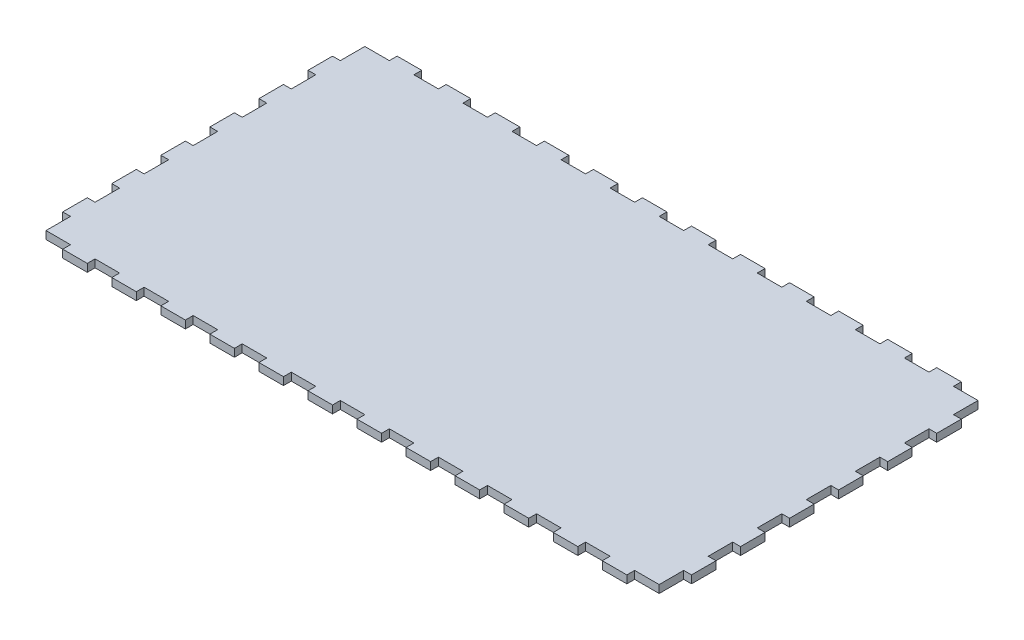
SolidWorks part; units mm, degrees
ref_plane "Plan de face" through (0, 0, 0) normal (0, 0, 1) x (1, 0, 0)
ref_plane "Plan de dessus" through (0, 0, 0) normal (0, 1, 0) x (1, 0, 0)
ref_plane "Plan de droite" through (0, 0, 0) normal (1, 0, 0) x (0, 0, -1)
sketch "Esquisse1" plane through (0, 0, 0) normal (0, 1, 0) x (1, 0, 0)
  line L1 (0, 0) -> (250, 0)
  line L2 (0, 0) -> (0, 130)
  line L3 (0, 130) -> (250, 130)
  line L4 (250, 0) -> (250, 130)
  dimension "D1" = 250
  dimension "D2" = 130
extrude "Boss.-Extru.1" add sketch "Esquisse1" along normal blind 3.175
sketch "Esquisse2" plane through (0, 3.175, 0) normal (0, 1, 0) x (1, 0, 0)
  line L0 (250, 130) -> (0, 130) construction
  line L1 (10, 130) -> (20, 130)
  line L2 (10, 130) -> (10, 133.175)
  line L3 (10, 133.175) -> (20, 133.175)
  line L4 (20, 130) -> (20, 133.175)
  line L5 (0, 130) -> (0, 0) construction
  line L6 (0, 0) -> (250, 0) construction
  line L7 (10, 0) -> (20, 0)
  line L8 (10, 0) -> (10, -3.175)
  line L9 (10, -3.175) -> (20, -3.175)
  line L10 (20, 0) -> (20, -3.175)
  dimension "D1" = 3.175
  dimension "D2" = 10
  dimension "D3" = 10
  dimension "D4" = 10
  dimension "D5" = 3.175
extrude "Boss.-Extru.2" add sketch "Esquisse2" against normal blind 3.175
pattern_linear "Répétition linéaire1" count 12 spacing 20 along (1, 0, 0) of "Boss.-Extru.2"
sketch "Esquisse3" plane through (0, 3.175, 0) normal (0, 1, 0) x (1, 0, 0)
  line L0 (250, 0) -> (250, 130) construction
  line L1 (250, 120) -> (253.175, 120)
  line L2 (250, 120) -> (250, 110)
  line L3 (250, 110) -> (253.175, 110)
  line L4 (253.175, 120) -> (253.175, 110)
  line L5 (250, 130) -> (240, 130) construction
  line L6 (0, 130) -> (0, 0) construction
  line L7 (0, 120) -> (-3.175, 120)
  line L8 (0, 120) -> (0, 110)
  line L9 (0, 110) -> (-3.175, 110)
  line L10 (-3.175, 120) -> (-3.175, 110)
  dimension "D1" = 10
  dimension "D2" = 10
  dimension "D3" = 3.175
  dimension "D4" = 10
  dimension "D5" = 3.175
extrude "Boss.-Extru.3" add sketch "Esquisse3" against normal blind 3.175
pattern_linear "Répétition linéaire2" count 6 spacing 20 along (0, 0, 1) of "Boss.-Extru.3"
